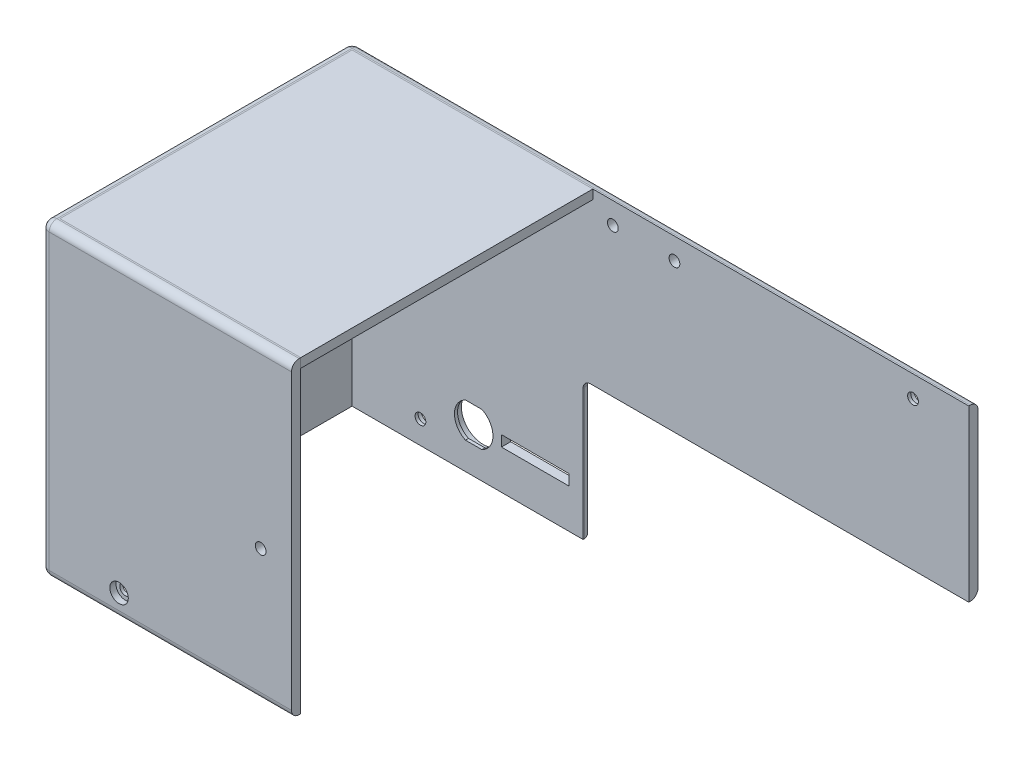
SolidWorks part; units mm, degrees
ref_plane "Front Plane" through (0, 0, 0) normal (0, 0, 1) x (1, 0, 0)
ref_plane "Top Plane" through (0, 0, 0) normal (0, 1, 0) x (1, 0, 0)
ref_plane "Right Plane" through (0, 0, 0) normal (1, 0, 0) x (0, 0, -1)
sketch "Sketch1" plane through (0, 0, 0) normal (0, 1, 0) x (1, 0, 0)
  line L0 (0, 0) -> (203.3, 0)
  line L1 (203.3, 0) -> (203.3, -3)
  line L2 (203.3, -3) -> (3, -3)
  line L5 (0, -100.9) -> (0, 0)
  line L9 (81.2, -100.9) -> (81.2, -97.9)
  line L11 (81.2, -97.9) -> (3, -97.9)
  line L12 (3, -97.9) -> (3, -3)
  line L13 (0, -100.9) -> (81.2, -100.9)
  dimension "D1" = 200.3
  dimension "D2" = 3
  dimension "D3" = 81.2
  dimension "D4" = 3
  dimension "D5" = 100.9
  dimension "D6" = 3
extrude "Main_Body" add sketch "Sketch1" along normal blind 100.2
sketch "Sketch3" plane through (0, 0, 0) normal (-1, 0, 0) x (0, 0, 1)
  line L0 (0, 0) -> (100.9, 0) construction
  line L1 (0, 100.2) -> (0, 0) construction
  line L2 (17.5, 7.5) -> (83.4, 7.5) construction
  line L3 (100.9, 100.2) -> (100.9, 0) construction
  circle A0 centre (83.4, 7.5) radius 1.75
  circle A1 centre (17.5, 7.5) radius 1.75
  dimension "D1" = 3.5
  dimension "D3" = 3.5
  dimension "D2" = 7.5
  dimension "D4" = 17.5
  dimension "D5" = 17.5
extrude "Left_Screw_Holes" [suppressed] cut sketch "Sketch3" against normal blind 10
sketch "Sketch4" [suppressed] plane through (0, 0, 0) normal (-1, 0, 0) x (0, 0, 1)
  circle A0 centre (17.5, 7.5) radius 3
  circle A1 centre (83.4, 7.5) radius 3
  dimension "D1" = 6
  dimension "D2" = 6
extrude "Left_Screw_Heads" [suppressed] cut sketch "Sketch4" against normal blind 2
sketch "Sketch5" plane through (0, 0, 0) normal (0, 0, -1) x (-1, 0, 0)
  line L0 (0, 100.2) -> (0, 0) construction
  line L1 (-203.3, 0) -> (0, 0) construction
  line L2 (-25.2, 7.5) -> (-185.2, 7.5) construction
  line L3 (-185.2, 7.5) -> (-185.2, 93.2) construction
  line L4 (-185.2, 93.2) -> (-185.2, 100.2) construction
  line L5 (-203.3, 100.2) -> (0, 100.2) construction
  circle A0 centre (-25.2, 7.5) radius 1.75
  circle A1 centre (-185.2, 7.5) radius 1.75
  circle A2 centre (-185.2, 93.2) radius 1.75
  dimension "D1" = 3.5
  dimension "D2" = 25.2
  dimension "D3" = 7.5
  dimension "D5" = 3.5
  dimension "D6" = 3.5
  dimension "D4" = 160
  dimension "D7" = 7
extrude "Back_Screw_Holes" cut sketch "Sketch5" against normal blind 10
sketch "Sketch12" plane through (0, 0, 0) normal (0, 0, -1) x (-1, 0, 0)
  circle A0 centre (-25.2, 7.5) radius 3
  circle A1 centre (-185.2, 7.5) radius 3
  circle A2 centre (-185.2, 93.2) radius 3
  dimension "D1" = 6
  dimension "D2" = 6
  dimension "D3" = 6
extrude "Back_Screw_Heads" cut sketch "Sketch12" against normal blind 2
sketch "Sketch6" plane through (0, 0, 3) normal (0, 0, 1) x (1, 0, 0)
  line L1 (78, 45) -> (298, 45)
  line L2 (78, 45) -> (78, 0)
  line L3 (78, 0) -> (298, 0)
  line L4 (298, 45) -> (298, 0)
  line L5 (3, 0) -> (203.3, 0) construction
  line L6 (0, 100.2) -> (0, 0) construction
  dimension "D1" = 45
  dimension "D2" = 220
  dimension "D4" = 78
extrude "Paper_Through_Hole" cut sketch "Sketch6" against normal blind 10
sketch "Sketch7" plane through (0, 0, 100.9) normal (0, 0, 1) x (1, 0, 0)
  line L0 (0, 0) -> (81.2, 0) construction
  line L1 (0, 100.2) -> (0, 0) construction
  circle A0 centre (25.2, 7.5) radius 1.75
  dimension "D1" = 3.5
  dimension "D2" = 7.5
  dimension "D3" = 25.2
extrude "Front_Left_Screw_Hole" cut sketch "Sketch7" against normal blind 10
sketch "Sketch8" plane through (0, 0, 100.9) normal (0, 0, 1) x (1, 0, 0)
  circle A0 centre (25.2, 7.5) radius 3
  dimension "D1" = 6
extrude "Front_Left_Screw_Head" cut sketch "Sketch8" against normal blind 2
sketch "Sketch9" plane through (0, 100.2, 0) normal (0, 1, 0) x (1, 0, 0)
  line L1 (81.2, -97.9) -> (3, -97.9)
  line L2 (81.2, -97.9) -> (81.2, -3)
  line L3 (81.2, -3) -> (3, -3)
  line L4 (3, -97.9) -> (3, -3)
extrude "Boss-Extrude1" add sketch "Sketch9" against normal blind 3 separate body
sketch "Sketch10" plane through (0, 0, 0) normal (0, 0, -1) x (-1, 0, 0)
  line L0 (-107.7, 93.2) -> (-87.7, 93.2) construction
  line L1 (-203.3, 100.2) -> (0, 100.2) construction
  line L2 (0, 93.2) -> (-87.7, 93.2) construction
  line L3 (0, 100.2) -> (0, 0) construction
  circle A0 centre (-107.7, 93.2) radius 1.75
  circle A1 centre (-87.7, 93.2) radius 1.75
  dimension "D1" = 20
  dimension "D3" = 3.5
  dimension "D4" = 3.5
  dimension "D2" = 7
  dimension "D5" = 87.7
extrude "Hinge_Holes" cut sketch "Sketch10" against normal blind 10
sketch "Sketch11" plane through (0, 0, 100.9) normal (0, 0, 1) x (1, 0, 0)
  line L0 (0, 0) -> (81.2, 0) construction
  line L1 (81.2, 100.2) -> (81.2, 0) construction
  circle A0 centre (71.2, 43) radius 1.75
  dimension "D1" = 43
  dimension "D3" = 3.5
  dimension "D2" = 10
extrude "Latch_Hole" cut sketch "Sketch11" against normal blind 10
fillet "Fillet3" radius 2.5 11 edges at (101.65, 100.2, 0) (0, 100.2, 50.45) (0, 50.1, 0) (0, 50.1, 100.9) (40.6, 0, 100.9) (39, 0, 0) (0, 0, 50.45) (40.6, 100.2, 100.9) (140.65, 45, 0) (78, 45, 1.5) (78, 22.5, 0)
sketch "Sketch13" plane through (0, 0, 0) normal (0, 0, -1) x (-1, 0, 0)
  line L0 (-75.5, 2.5) -> (-2.5, 2.5) construction
  line L1 (-2.5, 2.5) -> (-2.5, 97.7) construction
  circle A0 centre (-42.5, 14.5) radius 7
  dimension "D1" = 14
  dimension "D2" = 12
  dimension "D3" = 40
extrude "Barre_Jack_Outer_Cutout" cut sketch "Sketch13" against normal blind 2
sketch "Sketch14" plane through (0, 0, 2) normal (0, 0, -1) x (-1, 0, 0)
  line L0 (-45.1721, 20.15) -> (-39.8279, 20.15)
  line L1 (-39.8279, 8.85) -> (-45.1721, 8.85)
  arc A0 (-39.8279, 20.15) -> (-39.8279, 8.85) centre (-42.5, 14.5) cw
  arc A1 (-45.1721, 8.85) -> (-45.1721, 20.15) centre (-42.5, 14.5) cw
  circle A2 centre (-42.5, 14.5) radius 7 construction
  dimension "D1" = 6.25
  dimension "D3" = 6.25
  dimension "D2" = 11.3
extrude "Barrel_Jack_Inner_Cutout" cut sketch "Sketch14" against normal up to next (1 mm away)
sketch "Sketch15" plane through (0, 0, 0) normal (0, 0, -1) x (-1, 0, 0)
  line L0 (-49.5, 14.5) -> (-51.5, 14.5) construction
  line L1 (-73.5, 16.25) -> (-51.5, 16.25)
  line L2 (-73.5, 16.25) -> (-73.5, 12.75)
  line L3 (-73.5, 12.75) -> (-51.5, 12.75)
  line L4 (-51.5, 16.25) -> (-51.5, 12.75)
  line L5 (-73.5, 14.5) -> (-75.5, 14.5) construction
  line L6 (-75.5, 42.5) -> (-75.5, 2.5) construction
  circle A0 centre (-42.5, 14.5) radius 7 construction
  circle A1 centre (-42.5, 14.5) radius 7 construction
  point P12 (-51.5, 14.5)
  dimension "D1" = 3.5
  dimension "D2" = 22
extrude "Keyboard_Cable_Passthrough" cut sketch "Sketch15" against normal up to next (3 mm away)
